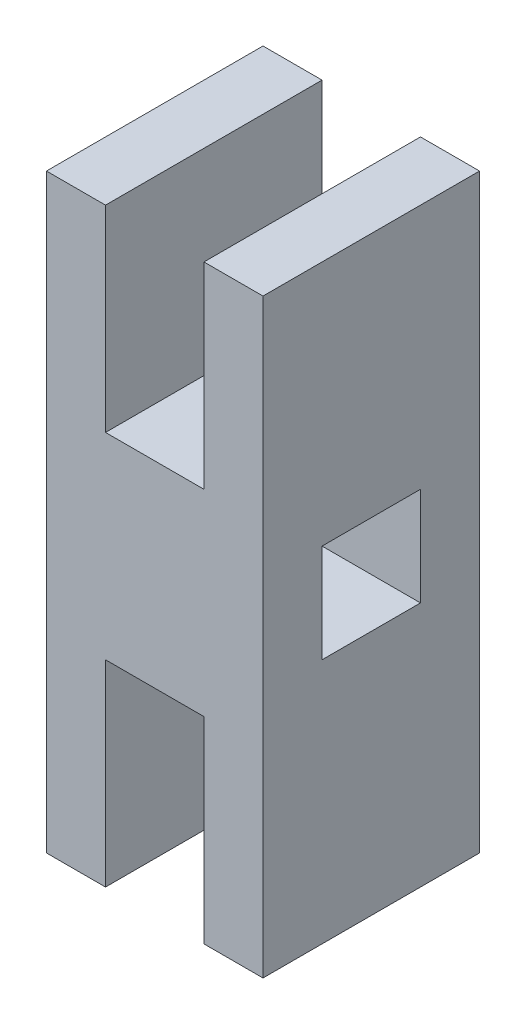
SolidWorks part; units mm, degrees
ref_plane "Front Plane" through (0, 0, 0) normal (0, 0, 1) x (1, 0, 0)
ref_plane "Top Plane" through (0, 0, 0) normal (0, 1, 0) x (1, 0, 0)
ref_plane "Right Plane" through (0, 0, 0) normal (1, 0, 0) x (0, 0, -1)
sketch "Sketch1" plane through (0, 0, 0) normal (0, 0, 1) x (1, 0, 0)
  line L0 (0, 0) -> (0, 32.984) construction
  line L1 (-2.5, 5) -> (2.5, 5)
  line L2 (2.5, 5) -> (2.5, 15)
  line L3 (2.5, 15) -> (5.5, 15)
  line L4 (5.5, 15) -> (5.5, -15)
  line L5 (0, 0) -> (11, 0) construction
  line L6 (-2.5, -5) -> (2.5, -5)
  line L7 (2.5, -15) -> (5.5, -15)
  line L8 (2.5, -5) -> (2.5, -15)
  line L9 (-2.5, -15) -> (-5.5, -15)
  line L10 (-2.5, -5) -> (-2.5, -15)
  line L11 (-5.5, 15) -> (-5.5, -15)
  line L12 (-2.5, 5) -> (-2.5, 15)
  line L13 (-2.5, 15) -> (-5.5, 15)
  point P5 (0, 0)
  point P13 (5.5, 0)
  point P17 (0, 5)
  point P18 (0, -5)
  dimension "D1" = 5
  dimension "D2" = 2.5
  dimension "D3" = 3
  dimension "D4" = 10
extrude "Boss-Extrude1" add sketch "Sketch1" along normal blind 10 and the other way blind 1
sketch "Sketch2" plane through (5.5, 0, 0) normal (1, 0, 0) x (0, 0, -1)
  line L0 (-10, 0) -> (1, 0) construction
  line L3 (-10, -15) -> (-10, 15) construction
  line L4 (1, -15) -> (1, 15) construction
  line L5 (-4.5, 15) -> (-4.5, -15) construction
  line L6 (1, 15) -> (-10, 15) construction
  line L7 (1, -15) -> (-10, -15) construction
  line L9 (-7, 2.5) -> (-2, 2.5)
  line L10 (-7, 2.5) -> (-7, -2.5)
  line L11 (-7, -2.5) -> (-2, -2.5)
  line L12 (-2, 2.5) -> (-2, -2.5)
  line L13 (-7, 2.5) -> (-2, -2.5) construction
  line L14 (-7, -2.5) -> (-2, 2.5) construction
  point P12 (-4.5, 0)
  dimension "D1" = 5
  dimension "D2" = 5
extrude "Cut-Extrude1" cut sketch "Sketch2" against normal through all both and the other way through all
